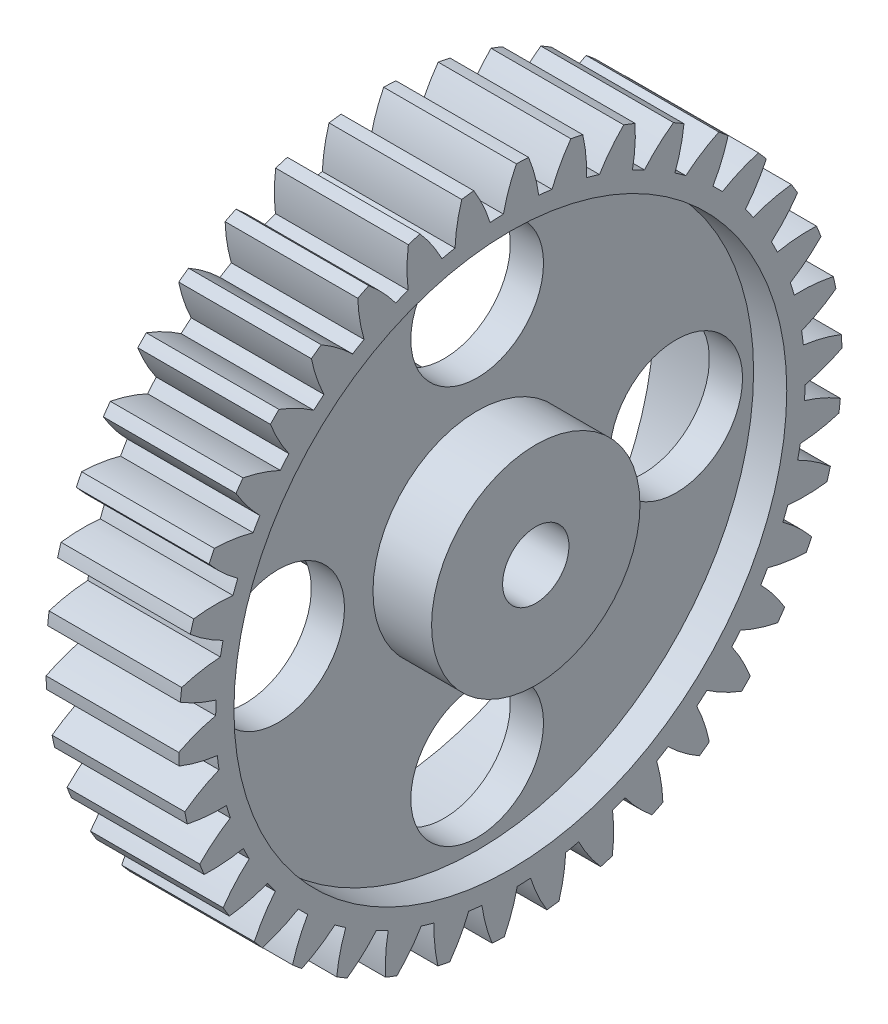
SolidWorks part; units mm, degrees
ref_plane "Front Plane" through (0, 0, 0) normal (0, 0, 1) x (1, 0, 0)
ref_plane "Top Plane" through (0, 0, 0) normal (0, 1, 0) x (1, 0, 0)
ref_plane "Right Plane" through (0, 0, 0) normal (1, 0, 0) x (0, 0, -1)
sketch "Sketch1" plane through (0, 0, 0) normal (1, 0, 0) x (0, 0, -1)
  line L0 (0, 0) -> (0.1096, 2.998) construction
  line L1 (0.9733, 26.6322) -> (1.0957, 29.98) construction
  circle A0 centre (0, 0) radius 30 construction
  circle A1 centre (0, 0) radius 28.75 construction
  circle A2 centre (0, 0) radius 26.65 construction
  circle A3 centre (0, 0) radius 3
  arc A4 (0, 28.75) -> (2.0986, 28.6733) centre (0, 0) cw
  arc A5 (-0.6274, 26.6426) -> (2.5705, 26.5257) centre (0, 0) cw
  arc A6 (0.5458, 29.995) -> (1.6451, 29.9549) centre (0, 0) cw
  arc A7 (1.6451, 29.9549) -> (2.5705, 26.5257) centre (-11.6684, 24.5227) cw
  arc A8 (0.5458, 29.995) -> (-0.6274, 26.6426) centre (13.4273, 23.6055) ccw
  arc A9 (5.4754, 29.4961) -> (3.7664, 26.3825) centre (17.1295, 21.0735) ccw
  arc A10 (3.7664, 26.3825) -> (6.9014, 25.7409) centre (0, 0) cw
  arc A11 (6.5531, 29.2755) -> (6.9014, 25.7409) centre (-7.4729, 26.1088) cw
  arc A12 (5.4754, 29.4961) -> (6.5531, 29.2755) centre (0, 0) cw
  arc A13 (10.2556, 28.1926) -> (8.0575, 25.4028) centre (20.3644, 17.9667) ccw
  arc A14 (8.0575, 25.4028) -> (11.0441, 24.2539) centre (0, 0) cw
  arc A15 (11.2823, 27.7977) -> (11.0441, 24.2539) centre (-3.0736, 26.9827) cw
  arc A16 (10.2556, 28.1926) -> (11.2823, 27.7977) centre (0, 0) cw
  arc A17 (14.7561, 26.1201) -> (12.1287, 23.7301) centre (23.0439, 14.3698) ccw
  arc A18 (12.1287, 23.7301) -> (14.8855, 22.1053) centre (0, 0) cw
  arc A19 (15.7038, 25.5615) -> (14.8855, 22.1053) centre (1.4095, 27.1206) cw
  arc A20 (14.7561, 26.1201) -> (15.7038, 25.5615) centre (0, 0) cw
  arc A21 (18.8541, 23.335) -> (15.8691, 21.4101) centre (25.0948, 10.3809) ccw
  arc A22 (15.8691, 21.4101) -> (18.3209, 19.3537) centre (0, 0) cw
  arc A23 (19.6969, 22.6282) -> (18.3209, 19.3537) centre (5.8542, 26.5187) cw
  arc A24 (18.8541, 23.335) -> (19.6969, 22.6282) centre (0, 0) cw
  arc A25 (22.4377, 19.9135) -> (19.1767, 18.5061) centre (26.4612, 6.1088) ccw
  arc A26 (19.1767, 18.5061) -> (21.2566, 16.0742) centre (0, 0) cw
  arc A27 (23.1527, 19.0775) -> (21.2566, 16.0742) centre (10.1392, 25.1934) cw
  arc A28 (22.4377, 19.9135) -> (23.1527, 19.0775) centre (0, 0) cw
  arc A29 (25.4094, 15.9488) -> (21.9612, 15.0974) centre (27.1058, 1.6702) ccw
  arc A30 (21.9612, 15.0974) -> (23.6124, 12.3563) centre (0, 0) cw
  arc A31 (25.977, 15.0065) -> (23.6124, 12.3563) centre (14.1476, 23.181) cw
  arc A32 (25.4094, 15.9488) -> (25.977, 15.0065) centre (0, 0) cw
  arc A33 (27.6879, 11.549) -> (24.1466, 11.2768) centre (27.011, -2.8141) ccw
  arc A34 (24.1466, 11.2768) -> (25.3241, 8.3013) centre (0, 0) cw
  arc A35 (28.0927, 10.5262) -> (25.3241, 8.3013) centre (17.7701, 20.5362) cw
  arc A36 (27.6879, 11.549) -> (28.0927, 10.5262) centre (0, 0) cw
  arc A37 (29.2112, 6.8342) -> (25.6733, 7.1486) centre (26.1794, -7.2216) ccw
  arc A38 (25.6733, 7.1486) -> (26.3451, 4.0199) centre (0, 0) cw
  arc A39 (29.4421, 5.7587) -> (26.3451, 4.0199) centre (20.9079, 17.3313) cw
  arc A40 (29.2112, 6.8342) -> (29.4421, 5.7587) centre (0, 0) cw
  arc A41 (29.9377, 1.933) -> (26.4998, 2.8254) centre (24.6337, -11.4321) ccw
  arc A42 (26.4998, 2.8254) -> (26.6474, -0.3712) centre (0, 0) cw
  arc A43 (29.9884, 0.8342) -> (26.6474, -0.3712) centre (23.4754, 13.6536) cw
  arc A44 (29.9377, 1.933) -> (29.9884, 0.8342) centre (0, 0) cw
  arc A45 (29.8475, -3.0209) -> (26.6034, -1.5749) centre (22.4161, -15.3307) ccw
  arc A46 (26.6034, -1.5749) -> (26.2229, -4.7522) centre (0, 0) cw
  arc A47 (29.7167, -4.1131) -> (26.2229, -4.7522) centre (25.4025, 9.6034) cw
  arc A48 (29.8475, -3.0209) -> (29.7167, -4.1131) centre (0, 0) cw
  arc A49 (28.9432, -7.8925) -> (25.9814, -5.9322) centre (19.587, -18.8112) ccw
  arc A50 (25.9814, -5.9322) -> (25.083, -9.0035) centre (0, 0) cw
  arc A51 (28.6344, -8.9482) -> (25.083, -9.0035) centre (26.6367, 5.2913) cw
  arc A52 (28.9432, -7.8925) -> (28.6344, -8.9482) centre (0, 0) cw
  arc A53 (27.2494, -12.5487) -> (24.6506, -10.1277) centre (16.2236, -21.7786) ccw
  arc A54 (24.6506, -10.1277) -> (23.259, -13.0092) centre (0, 0) cw
  arc A55 (26.771, -13.5393) -> (23.259, -13.0092) centre (27.1443, 0.8349) cw
  arc A56 (27.2494, -12.5487) -> (26.771, -13.5393) centre (0, 0) cw
  arc A57 (24.8123, -16.8627) -> (22.6474, -14.0469) centre (12.4177, -24.1518) ccw
  arc A58 (22.6474, -14.0469) -> (20.8005, -16.6601) centre (0, 0) cw
  arc A59 (24.1774, -17.761) -> (20.8005, -16.6601) centre (26.9115, -3.6443) cw
  arc A60 (24.8123, -16.8627) -> (24.1774, -17.761) centre (0, 0) cw
  arc A61 (21.6984, -20.7167) -> (20.0265, -17.583) centre (8.2731, -25.8663) ccw
  arc A62 (20.0265, -17.583) -> (17.7747, -19.8566) centre (0, 0) cw
  arc A63 (20.9243, -21.4982) -> (17.7747, -19.8566) centre (25.9447, -8.0241) cw
  arc A64 (21.6984, -20.7167) -> (20.9243, -21.4982) centre (0, 0) cw
  arc A65 (17.9926, -24.0056) -> (16.8593, -20.6394) centre (3.9028, -26.8753) ccw
  arc A66 (16.8593, -20.6394) -> (14.264, -22.5114) centre (0, 0) cw
  arc A67 (17.1004, -24.649) -> (14.264, -22.5114) centre (24.2701, -12.185) cw
  arc A68 (17.9926, -24.0056) -> (17.1004, -24.649) centre (0, 0) cw
  arc A69 (13.796, -26.6396) -> (13.2323, -23.1329) centre (-0.5739, -27.1511) ccw
  arc A70 (13.2323, -23.1329) -> (10.3642, -24.5521) centre (0, 0) cw
  arc A71 (12.8101, -27.1275) -> (10.3642, -24.5521) centre (21.9335, -16.0135) cw
  arc A72 (13.796, -26.6396) -> (12.8101, -27.1275) centre (0, 0) cw
  arc A73 (9.2231, -28.5471) -> (9.2442, -24.9953) centre (-5.035, -26.6863) ccw
  arc A74 (9.2442, -24.9953) -> (6.1817, -25.9231) centre (0, 0) cw
  arc A75 (8.1704, -28.866) -> (6.1817, -25.9231) centre (18.9986, -19.4053) cw
  arc A76 (9.2231, -28.5471) -> (8.1704, -28.866) centre (0, 0) cw
  arc A77 (4.3986, -29.6758) -> (5.0041, -26.176) centre (-9.3588, -25.4936) ccw
  arc A78 (5.0041, -26.176) -> (1.8306, -26.5871) centre (0, 0) cw
  arc A79 (3.3077, -29.8171) -> (1.8306, -26.5871) centre (15.5455, -22.2677) cw
  arc A80 (4.3986, -29.6758) -> (3.3077, -29.8171) centre (0, 0) cw
  arc A81 (-0.5458, -29.995) -> (0.6274, -26.6426) centre (-13.4273, -23.6055) ccw
  arc A82 (0.6274, -26.6426) -> (-2.5705, -26.5257) centre (0, 0) cw
  arc A83 (-1.6451, -29.9549) -> (-2.5705, -26.5257) centre (11.6684, -24.5227) cw
  arc A84 (-0.5458, -29.995) -> (-1.6451, -29.9549) centre (0, 0) cw
  arc A85 (-5.4754, -29.4961) -> (-3.7664, -26.3825) centre (-17.1295, -21.0735) ccw
  arc A86 (-3.7664, -26.3825) -> (-6.9014, -25.7409) centre (0, 0) cw
  arc A87 (-6.5531, -29.2755) -> (-6.9014, -25.7409) centre (7.4729, -26.1088) cw
  arc A88 (-5.4754, -29.4961) -> (-6.5531, -29.2755) centre (0, 0) cw
  arc A89 (-10.2556, -28.1926) -> (-8.0575, -25.4028) centre (-20.3644, -17.9667) ccw
  arc A90 (-8.0575, -25.4028) -> (-11.0441, -24.2539) centre (0, 0) cw
  arc A91 (-11.2823, -27.7977) -> (-11.0441, -24.2539) centre (3.0736, -26.9827) cw
  arc A92 (-10.2556, -28.1926) -> (-11.2823, -27.7977) centre (0, 0) cw
  arc A93 (-14.7561, -26.1201) -> (-12.1287, -23.7301) centre (-23.0439, -14.3698) ccw
  arc A94 (-12.1287, -23.7301) -> (-14.8855, -22.1053) centre (0, 0) cw
  arc A95 (-15.7038, -25.5615) -> (-14.8855, -22.1053) centre (-1.4095, -27.1206) cw
  arc A96 (-14.7561, -26.1201) -> (-15.7038, -25.5615) centre (0, 0) cw
  arc A97 (-18.8541, -23.335) -> (-15.8691, -21.4101) centre (-25.0948, -10.3809) ccw
  arc A98 (-15.8691, -21.4101) -> (-18.3209, -19.3537) centre (0, 0) cw
  arc A99 (-19.6969, -22.6282) -> (-18.3209, -19.3537) centre (-5.8542, -26.5187) cw
  arc A100 (-18.8541, -23.335) -> (-19.6969, -22.6282) centre (0, 0) cw
  arc A101 (-22.4377, -19.9135) -> (-19.1767, -18.5061) centre (-26.4612, -6.1088) ccw
  arc A102 (-19.1767, -18.5061) -> (-21.2566, -16.0742) centre (0, 0) cw
  arc A103 (-23.1527, -19.0775) -> (-21.2566, -16.0742) centre (-10.1392, -25.1934) cw
  arc A104 (-22.4377, -19.9135) -> (-23.1527, -19.0775) centre (0, 0) cw
  arc A105 (-25.4094, -15.9488) -> (-21.9612, -15.0974) centre (-27.1058, -1.6702) ccw
  arc A106 (-21.9612, -15.0974) -> (-23.6124, -12.3563) centre (0, 0) cw
  arc A107 (-25.977, -15.0065) -> (-23.6124, -12.3563) centre (-14.1476, -23.181) cw
  arc A108 (-25.4094, -15.9488) -> (-25.977, -15.0065) centre (0, 0) cw
  arc A109 (-27.6879, -11.549) -> (-24.1466, -11.2768) centre (-27.011, 2.8141) ccw
  arc A110 (-24.1466, -11.2768) -> (-25.3241, -8.3013) centre (0, 0) cw
  arc A111 (-28.0927, -10.5262) -> (-25.3241, -8.3013) centre (-17.7701, -20.5362) cw
  arc A112 (-27.6879, -11.549) -> (-28.0927, -10.5262) centre (0, 0) cw
  arc A113 (-29.2112, -6.8342) -> (-25.6733, -7.1486) centre (-26.1794, 7.2216) ccw
  arc A114 (-25.6733, -7.1486) -> (-26.3451, -4.0199) centre (0, 0) cw
  arc A115 (-29.4421, -5.7587) -> (-26.3451, -4.0199) centre (-20.9079, -17.3313) cw
  arc A116 (-29.2112, -6.8342) -> (-29.4421, -5.7587) centre (0, 0) cw
  arc A117 (-29.9377, -1.933) -> (-26.4998, -2.8254) centre (-24.6337, 11.4321) ccw
  arc A118 (-26.4998, -2.8254) -> (-26.6474, 0.3712) centre (0, 0) cw
  arc A119 (-29.9884, -0.8342) -> (-26.6474, 0.3712) centre (-23.4754, -13.6536) cw
  arc A120 (-29.9377, -1.933) -> (-29.9884, -0.8342) centre (0, 0) cw
  arc A121 (-29.8475, 3.0209) -> (-26.6034, 1.5749) centre (-22.4161, 15.3307) ccw
  arc A122 (-26.6034, 1.5749) -> (-26.2229, 4.7522) centre (0, 0) cw
  arc A123 (-29.7167, 4.1131) -> (-26.2229, 4.7522) centre (-25.4025, -9.6034) cw
  arc A124 (-29.8475, 3.0209) -> (-29.7167, 4.1131) centre (0, 0) cw
  arc A125 (-28.9432, 7.8925) -> (-25.9814, 5.9322) centre (-19.587, 18.8112) ccw
  arc A126 (-25.9814, 5.9322) -> (-25.083, 9.0035) centre (0, 0) cw
  arc A127 (-28.6344, 8.9482) -> (-25.083, 9.0035) centre (-26.6367, -5.2913) cw
  arc A128 (-28.9432, 7.8925) -> (-28.6344, 8.9482) centre (0, 0) cw
  arc A129 (-27.2494, 12.5487) -> (-24.6506, 10.1277) centre (-16.2236, 21.7786) ccw
  arc A130 (-24.6506, 10.1277) -> (-23.259, 13.0092) centre (0, 0) cw
  arc A131 (-26.771, 13.5393) -> (-23.259, 13.0092) centre (-27.1443, -0.8349) cw
  arc A132 (-27.2494, 12.5487) -> (-26.771, 13.5393) centre (0, 0) cw
  arc A133 (-24.8123, 16.8627) -> (-22.6474, 14.0469) centre (-12.4177, 24.1518) ccw
  arc A134 (-22.6474, 14.0469) -> (-20.8005, 16.6601) centre (0, 0) cw
  arc A135 (-24.1774, 17.761) -> (-20.8005, 16.6601) centre (-26.9115, 3.6443) cw
  arc A136 (-24.8123, 16.8627) -> (-24.1774, 17.761) centre (0, 0) cw
  arc A137 (-21.6984, 20.7167) -> (-20.0265, 17.583) centre (-8.2731, 25.8663) ccw
  arc A138 (-20.0265, 17.583) -> (-17.7747, 19.8566) centre (0, 0) cw
  arc A139 (-20.9243, 21.4982) -> (-17.7747, 19.8566) centre (-25.9447, 8.0241) cw
  arc A140 (-21.6984, 20.7167) -> (-20.9243, 21.4982) centre (0, 0) cw
  arc A141 (-17.9926, 24.0056) -> (-16.8593, 20.6394) centre (-3.9028, 26.8753) ccw
  arc A142 (-16.8593, 20.6394) -> (-14.264, 22.5114) centre (0, 0) cw
  arc A143 (-17.1004, 24.649) -> (-14.264, 22.5114) centre (-24.2701, 12.185) cw
  arc A144 (-17.9926, 24.0056) -> (-17.1004, 24.649) centre (0, 0) cw
  arc A145 (-13.796, 26.6396) -> (-13.2323, 23.1329) centre (0.5739, 27.1511) ccw
  arc A146 (-13.2323, 23.1329) -> (-10.3642, 24.5521) centre (0, 0) cw
  arc A147 (-12.8101, 27.1275) -> (-10.3642, 24.5521) centre (-21.9335, 16.0135) cw
  arc A148 (-13.796, 26.6396) -> (-12.8101, 27.1275) centre (0, 0) cw
  arc A149 (-9.2231, 28.5471) -> (-9.2442, 24.9953) centre (5.035, 26.6863) ccw
  arc A150 (-9.2442, 24.9953) -> (-6.1817, 25.9231) centre (0, 0) cw
  arc A151 (-8.1704, 28.866) -> (-6.1817, 25.9231) centre (-18.9986, 19.4053) cw
  arc A152 (-9.2231, 28.5471) -> (-8.1704, 28.866) centre (0, 0) cw
  arc A153 (-4.3986, 29.6758) -> (-5.0041, 26.176) centre (9.3588, 25.4936) ccw
  arc A154 (-5.0041, 26.176) -> (-1.8306, 26.5871) centre (0, 0) cw
  arc A155 (-3.3077, 29.8171) -> (-1.8306, 26.5871) centre (-15.5455, 22.2677) cw
  arc A156 (-4.3986, 29.6758) -> (-3.3077, 29.8171) centre (0, 0) cw
  circle A229 centre (0, 0) radius 26.65
  circle A230 centre (0, 0) radius 18 construction
  circle A231 centre (0, 18) radius 6
  circle A232 centre (18, 0) radius 6
  circle A233 centre (0, -18) radius 6
  circle A234 centre (-18, 0) radius 6
  point P13 (0.9733, 26.6322)
  point P16 (1.0957, 29.98)
  point P254 (0, 0)
  point P351 (0, 0)
  dimension "D1" = 60
  dimension "D2" = 57.5
  dimension "D3" = 53.3
  dimension "D4" = 6
  dimension "D5" = 2.1
  dimension "D9" = 53.3
  dimension "D10" = 4
  dimension "D6" = 3.2
  dimension "D7" = 1.1
  dimension "D8" = 38
extrude "Boss-Extrude1" add sketch "Sketch1" along normal blind 12
sketch "Sketch2" plane through (12, 0, 0) normal (1, 0, 0) x (0, 0, -1)
  circle A0 centre (0, 0) radius 9.425
  circle A1 centre (0, 0) radius 3
  dimension "D1" = 6
  dimension "D2" = 18.85
extrude "Boss-Extrude2" add sketch "Sketch2" along normal blind 2.3 and the other way blind 3
sketch "Sketch3" plane through (0, 0, 0) normal (-1, 0, 0) x (0, 0, 1)
  circle A0 centre (0, 0) radius 7.325
  circle A1 centre (0, 0) radius 3
  dimension "D1" = 6
  dimension "D2" = 14.65
extrude "Boss-Extrude3" add sketch "Sketch3" along normal blind 8.3 and the other way blind 6
sketch "Sketch4" plane through (12, 0, 0) normal (1, 0, 0) x (0, 0, -1)
  circle A0 centre (0, 0) radius 25
  circle A1 centre (0, 0) radius 9.425
extrude "Cut-Extrude1" cut sketch "Sketch4" against normal blind 3
sketch "Sketch5" plane through (0, 0, 0) normal (-1, 0, 0) x (0, 0, 1)
  circle A0 centre (0, 0) radius 25
  circle A1 centre (0, 0) radius 7.325
extrude "Cut-Extrude2" cut sketch "Sketch5" against normal blind 6
